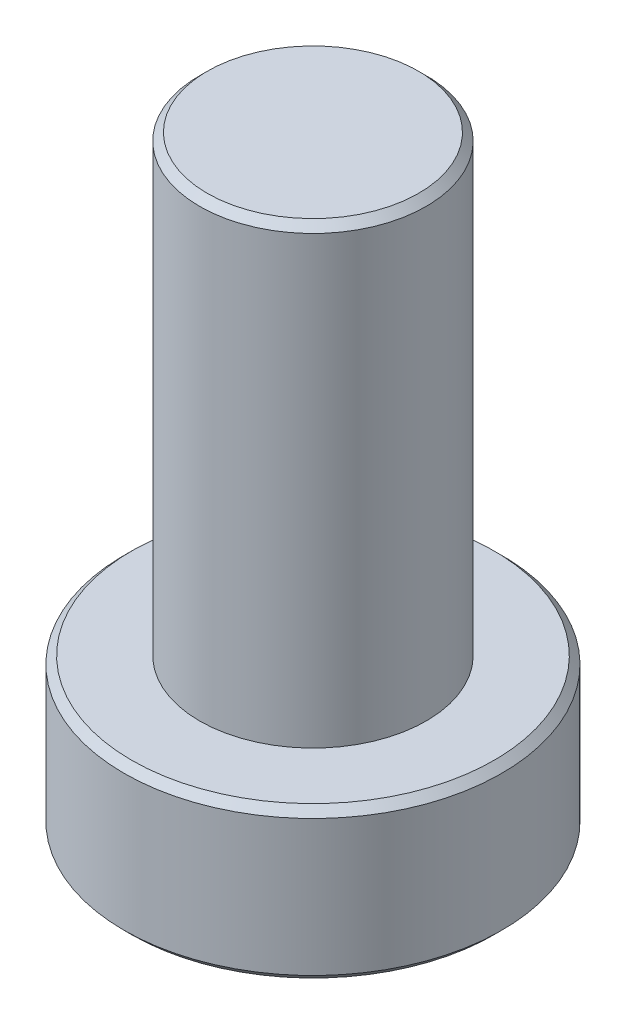
SolidWorks part; units mm, degrees
ref_plane "Спереди" through (0, 0, 0) normal (0, 0, 1) x (1, 0, 0)
ref_plane "Сверху" through (0, 0, 0) normal (0, 1, 0) x (1, 0, 0)
ref_plane "Справа" through (0, 0, 0) normal (1, 0, 0) x (0, 0, -1)
sketch "Эскиз1" plane through (0, 0, 0) normal (0, 1, 0) x (1, 0, 0)
  circle A0 centre (0, 0) radius 5
  dimension "D1" = 10
extrude "Бобышка-Вытянуть1" add sketch "Эскиз1" along normal blind 4
sketch "Эскиз2" plane through (0, 4, 0) normal (0, 1, 0) x (1, 0, 0)
  circle A0 centre (0, 0) radius 3
  dimension "D1" = 6
extrude "Бобышка-Вытянуть2" add sketch "Эскиз2" along normal blind 12
chamfer "Фаска1" distance 0.2 angle 45 3 edges at (0, 0, 5) (0, 4, 5) (0, 16, 3)
